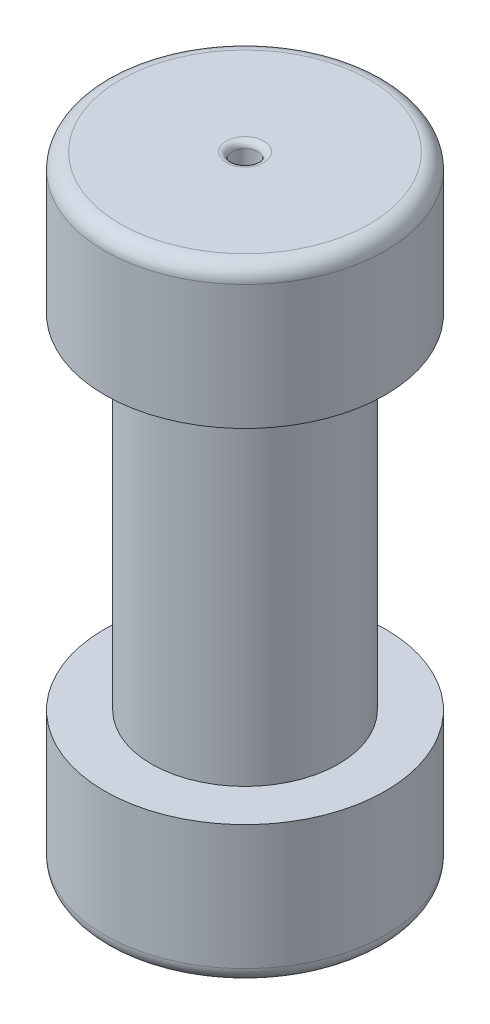
SolidWorks part; units mm, degrees
ref_plane "Front Plane" through (0, 0, 0) normal (0, 0, 1) x (1, 0, 0)
ref_plane "Top Plane" through (0, 0, 0) normal (0, 1, 0) x (1, 0, 0)
ref_plane "Right Plane" through (0, 0, 0) normal (1, 0, 0) x (0, 0, -1)
sketch "Sketch1" plane through (0, 0, 0) normal (0, 1, 0) x (1, 0, 0)
  circle A0 centre (0, 0) radius 22.86
  dimension "D1" = 45.72
extrude "Boss-Extrude1" add sketch "Sketch1" along normal blind 22.86
sketch "Sketch3" plane through (0, 22.86, 0) normal (0, 1, 0) x (1, 0, 0)
  circle A0 centre (0, 0) radius 15.24
  dimension "D1" = 30.48
extrude "Boss-Extrude2" add sketch "Sketch3" along normal blind 55.88
sketch "Sketch4" plane through (0, 78.74, 0) normal (0, 1, 0) x (1, 0, 0)
  circle A0 centre (0, 0) radius 22.86
  dimension "D1" = 45.72
extrude "Boss-Extrude3" add sketch "Sketch4" along normal blind 22.86
fillet "Fillet3" radius 2.54 2 edges at (0, 0, 22.86) (0, 101.6, 22.86)
sketch "Sketch5" plane through (0, 101.6, 0) normal (0, 1, 0) x (1, 0, 0)
  circle A0 centre (0, 0) radius 2.055
  dimension "D1" = 4.11
extrude "Cut-Extrude1" cut sketch "Sketch5" against normal blind 7.62
sketch "Sketch8" plane through (0, 0, 0) normal (0, -1, 0) x (1, 0, 0)
  line L1 (-1.85, 1.7) -> (1.85, 1.7)
  line L2 (-1.85, 1.7) -> (-1.85, -1.7)
  line L3 (-1.85, -1.7) -> (1.85, -1.7)
  line L4 (1.85, 1.7) -> (1.85, -1.7)
  point P4 (0, 0)
  point P5 (0, 1.7)
  dimension "D1" = 1.85
  dimension "D2" = 1.85
  dimension "D3" = 1.7
  dimension "D4" = 1.7
extrude "Cut-Extrude2" cut sketch "Sketch8" against normal blind 85
fillet "Fillet4" radius 1 5 edges at (-1.85, 0, 0) (0, 0, -1.7) (1.85, 0, 0) (0, 0, 1.7) (0, 101.6, 2.055)
